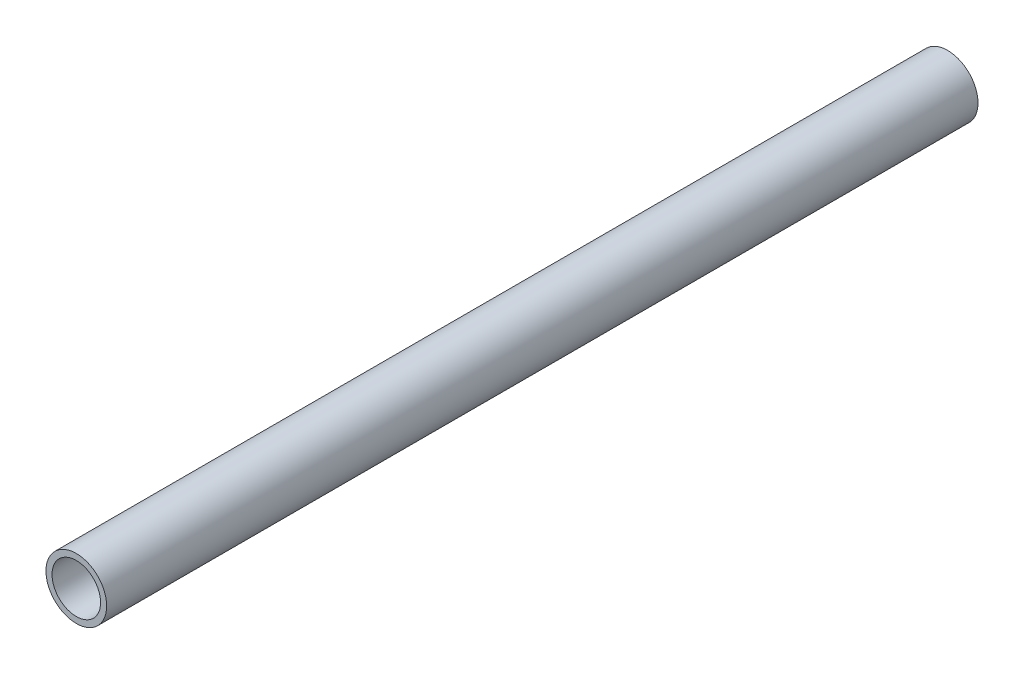
SolidWorks part; units mm, degrees
ref_plane "Front Plane" through (0, 0, 0) normal (0, 0, 1) x (1, 0, 0)
ref_plane "Top Plane" through (0, 0, 0) normal (0, 1, 0) x (1, 0, 0)
ref_plane "Right Plane" through (0, 0, 0) normal (1, 0, 0) x (0, 0, -1)
sketch "Sketch2" plane through (0, 0, 0) normal (0, 0, 1) x (1, 0, 0)
  circle A0 centre (0, 0) radius 5
  circle A1 centre (0, 0) radius 4
  dimension "D1" = 10
  dimension "D2" = 8
extrude "Boss-Extrude2" add sketch "Sketch2" along normal blind 143.5
